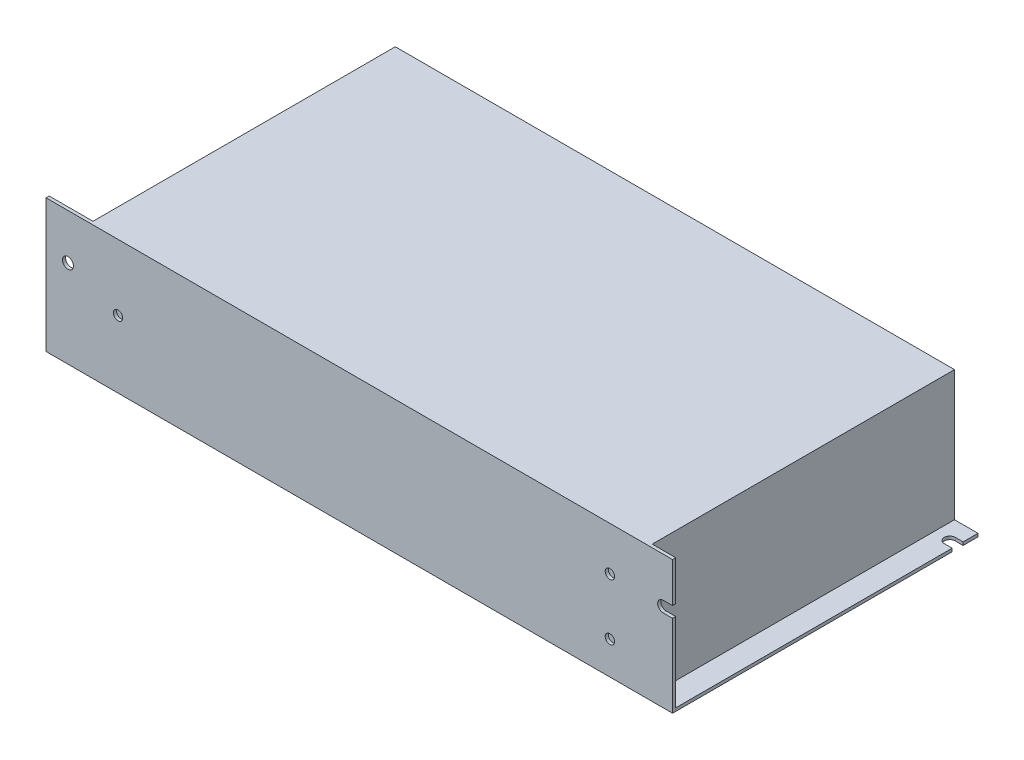
SolidWorks part; units mm, degrees
ref_plane "Front Plane" through (0, 0, 0) normal (0, 0, 1) x (1, 0, 0)
ref_plane "Top Plane" through (0, 0, 0) normal (0, 1, 0) x (1, 0, 0)
ref_plane "Right Plane" through (0, 0, 0) normal (1, 0, 0) x (0, 0, -1)
sketch "Sketch1" plane through (0, 0, 0) normal (0, 1, 0) x (1, 0, 0)
  line L0 (197.5, 92.75) -> (200, 92.75)
  line L1 (0, 0) -> (200, 0)
  line L2 (0, 0) -> (0, 97.5)
  line L3 (0, 97.5) -> (200, 97.5)
  line L4 (200, 0) -> (200, 89.25)
  line L5 (0, 0) -> (200, 97.5) construction
  line L6 (0, 97.5) -> (200, 0) construction
  line L7 (197.5, 89.25) -> (200, 89.25)
  line L9 (200, 92.75) -> (200, 97.5)
  arc A0 (197.5, 92.75) -> (197.5, 89.25) centre (197.5, 91) ccw
  circle A1 centre (3, 7.5) radius 1.5
  point P4 (100, 48.75)
  dimension "D6" = 3
  dimension "D7" = 3.5
  dimension "D1" = 200
  dimension "D2" = 97.5
  dimension "D3" = 6.5
  dimension "D4" = 2.5
  dimension "D5" = 7.5
  dimension "D8" = 3
extrude "Boss-Extrude1" add sketch "Sketch1" along normal blind 42.5
sketch "Sketch2" plane through (0, 42.5, 0) normal (0, 1, 0) x (1, 0, 0)
  line L0 (0, 0) -> (200, 0) construction
  line L1 (200, 97.5) -> (192.5, 97.5)
  line L2 (200, 97.5) -> (200, 1)
  line L3 (200, 1) -> (192.5, 1)
  line L4 (192.5, 97.5) -> (192.5, 1)
  line L5 (200, 97.5) -> (192.5, 1) construction
  line L6 (200, 1) -> (192.5, 97.5) construction
  line L8 (0, 97.5) -> (14, 97.5)
  line L9 (0, 97.5) -> (0, 1)
  line L10 (0, 1) -> (14, 1)
  line L11 (14, 97.5) -> (14, 1)
  line L12 (0, 97.5) -> (14, 1) construction
  line L13 (0, 1) -> (14, 97.5) construction
  point P4 (196.25, 49.25)
  point P15 (7, 49.25)
  dimension "D1" = 7.5
  dimension "D2" = 1
  dimension "D3" = 14
  dimension "D4" = 1
extrude "Cut-Extrude1" cut sketch "Sketch2" against normal offset from surface (41.5 mm away) 1 contours L11 L10 L9 L8 | L2 L3 L4 L1 up to face at (149.1562, 0, -69.875)
sketch "Sketch3" plane through (0, 0, 0) normal (0, 0, 1) x (1, 0, 0)
  line L0 (0, 42.5) -> (0, 0) construction
  line L1 (0, 0) -> (200, 0) construction
  line L4 (200, 42.5) -> (200, 0) construction
  line L5 (197, 29.75) -> (200, 29.75)
  line L6 (200, 29.75) -> (200, 26.25)
  line L7 (200, 26.25) -> (197, 26.25)
  circle A0 centre (7, 28) radius 1.75
  arc A1 (197, 29.75) -> (197, 26.25) centre (197, 28) ccw
  dimension "D1" = 7
  dimension "D3" = 3.5
  dimension "D2" = 28
  dimension "D4" = 3
extrude "Cut-Extrude2" cut sketch "Sketch3" against normal up to next
sketch "Sketch4" plane through (0, 1, 0) normal (0, 1, 0) x (1, 0, 0)
  line L0 (14, 97.5) -> (14, 1) construction
  line L1 (14, 87.5) -> (0, 87.5)
  line L2 (14, 87.5) -> (14, 12.5)
  line L3 (14, 12.5) -> (0, 12.5)
  line L4 (0, 87.5) -> (0, 12.5)
  line L5 (14, 87.5) -> (0, 12.5) construction
  line L6 (14, 12.5) -> (0, 87.5) construction
  line L7 (0, 1) -> (0, 97.5) construction
  line L8 (14, 97.5) -> (0, 97.5) construction
  line L9 (0, 0) -> (200, 0) construction
  point P4 (7, 50)
  dimension "D1" = 10
  dimension "D2" = 12.5
extrude "Boss-Extrude2" add sketch "Sketch4" along normal blind 23
sketch "Sketch5" plane through (0, 0, 0) normal (0, 0, 1) x (1, 0, 0)
  line L0 (0, 42.5) -> (0, 0) construction
  line L1 (200, 26.25) -> (200, 0) construction
  line L2 (0, 42.5) -> (200, 42.5) construction
  circle A0 centre (23, 21.5) radius 1.5
  circle A1 centre (180, 10.5) radius 1.5
  circle A2 centre (180, 28.5) radius 1.5
  dimension "D3" = 3
  dimension "D1" = 23
  dimension "D2" = 21
  dimension "D4" = 20
  dimension "D5" = 14
  dimension "D6" = 18
extrude "Cut-Extrude3" cut sketch "Sketch5" against normal blind 1
sketch "Sketch6" plane through (0, 0, 0) normal (0, -1, 0) x (1, 0, 0)
  line L0 (0, -97.5) -> (0, 0) construction
  line L1 (200, -97.5) -> (0, -97.5) construction
  circle A0 centre (5, -92.5) radius 1.5
  circle A1 centre (60, -9.5) radius 1.5
  circle A2 centre (60, -89.5) radius 1.5
  circle A3 centre (180, -89.5) radius 1.5
  circle A4 centre (180, -9.5) radius 1.5
  circle A5 centre (172.5, -92.5) radius 1.5
  dimension "D3" = 3
  dimension "D1" = 5
  dimension "D2" = 5
  dimension "D4" = 60
  dimension "D5" = 120
  dimension "D6" = 8
  dimension "D7" = 5
  dimension "D8" = 172.5
  dimension "D9" = 80
extrude "Cut-Extrude4" cut sketch "Sketch6" against normal blind 1
